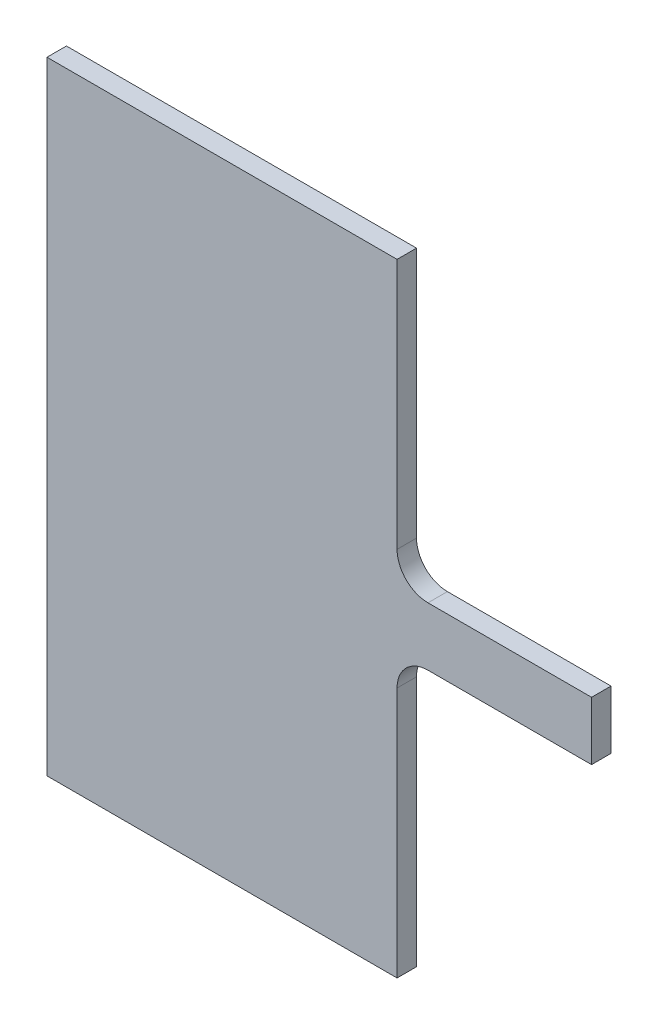
SolidWorks part; units mm, degrees
material "6061-T4 (SS)"
ref_plane "Front Plane" through (0, 0, 0) normal (0, 0, 1) x (1, 0, 0)
ref_plane "Top Plane" through (0, 0, 0) normal (0, 1, 0) x (1, 0, 0)
ref_plane "Right Plane" through (0, 0, 0) normal (1, 0, 0) x (0, 0, -1)
sketch "Sketch1" plane through (0, 0, 0) normal (0, 0, 1) x (1, 0, 0)
  line L3 (15.5494, 25) -> (29.7363, 25) construction
  line L6 (29.7363, -7) -> (11.7363, -7)
  line L7 (31.3238, 7.5) -> (39.7363, 7.5)
  line L8 (39.7363, 7.5) -> (39.7363, 10.5)
  line L9 (39.7363, 10.5) -> (31.3238, 10.5)
  line L10 (29.7363, -7) -> (29.7363, 5.9125)
  line L11 (29.7363, 12.0875) -> (29.7363, 25)
  line L12 (11.7363, -7) -> (11.7363, 25)
  line L13 (11.7363, 25) -> (29.7363, 25)
  arc A0 (31.3238, 10.5) -> (29.7363, 12.0875) centre (31.3238, 12.0875) cw
  arc A1 (31.3238, 7.5) -> (29.7363, 5.9125) centre (31.3238, 5.9125) ccw
  point P3 (29.7363, 10.5)
  point P14 (29.7363, 7.5)
  dimension "D6" = 1.5875
  dimension "D1" = 3
  dimension "D2" = 14.5
  dimension "D3" = 10
  dimension "D4" = 18
  dimension "D5" = 32
extrude "Boss-Extrude1" add sketch "Sketch1" along normal blind 1
